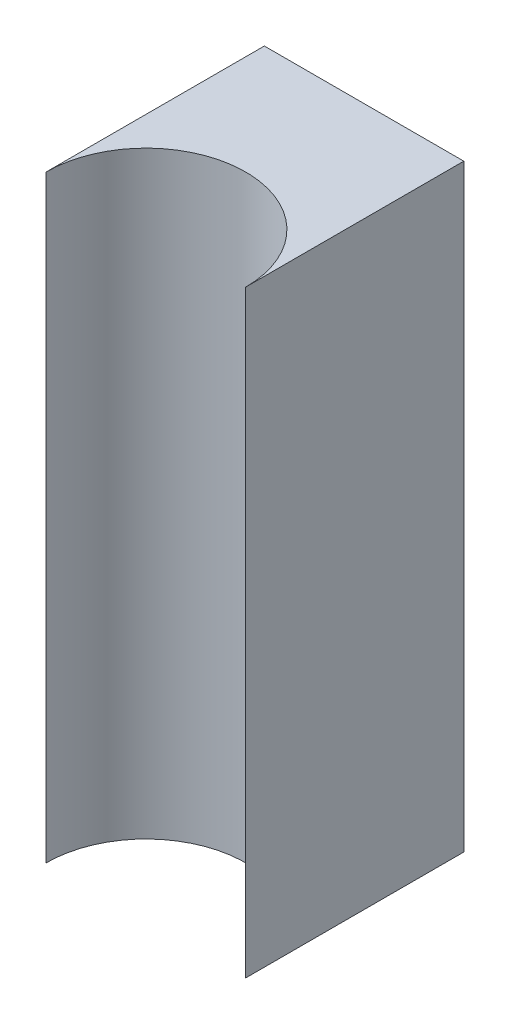
SolidWorks part; units mm, degrees
ref_plane "Front Plane" through (0, 0, 0) normal (0, 0, 1) x (1, 0, 0)
ref_plane "Top Plane" through (0, 0, 0) normal (0, 1, 0) x (1, 0, 0)
ref_plane "Right Plane" through (0, 0, 0) normal (1, 0, 0) x (0, 0, -1)
sketch "Sketch1" plane through (0, 0, 0) normal (0, 0, 1) x (1, 0, 0)
  line L1 (164, 22.5) -> (179, 22.5)
  line L2 (164, 22.5) -> (164, -22.5)
  line L3 (164, -22.5) -> (179, -22.5)
  line L4 (179, 22.5) -> (179, -22.5)
  line L5 (164, 22.5) -> (179, -22.5) construction
  line L6 (164, -22.5) -> (179, 22.5) construction
  point P4 (171.5, 0)
  dimension "D1" = 45
  dimension "D2" = 15
extrude "Boss-Extrude1" add sketch "Sketch1" along normal blind 22 contours L4 L3 L2 L1
sketch "Sketch2" plane through (0, -22.5, 0) normal (0, -1, 0) x (1, 0, 0)
  line L0 (171.5, 16.4063) -> (171.5, 0) construction
  line L4 (164, 0) -> (179, 0)
  line L5 (179, 0) -> (179, 22)
  line L6 (179, 22) -> (164, 22)
  line L7 (164, 22) -> (164, 0)
  line L8 (164, 0) -> (179, 0)
  line L9 (179, 0) -> (179, 22)
  line L10 (179, 22) -> (164, 22)
  line L11 (164, 22) -> (164, 0)
  circle A0 centre (171.5, 16.4063) radius 7.5
  line M3 (179, 22) -> (164, 22)
  line M4 (164, 22) -> (164, 0)
  dimension "D2" = 15
  dimension "D3" = 16.4063
  dimension "D1" = 0
extrude "Cut-Extrude1" cut sketch "Sketch2" against normal through all contours A0 L10 | A0 M3 M4 | A0 L9 M3
